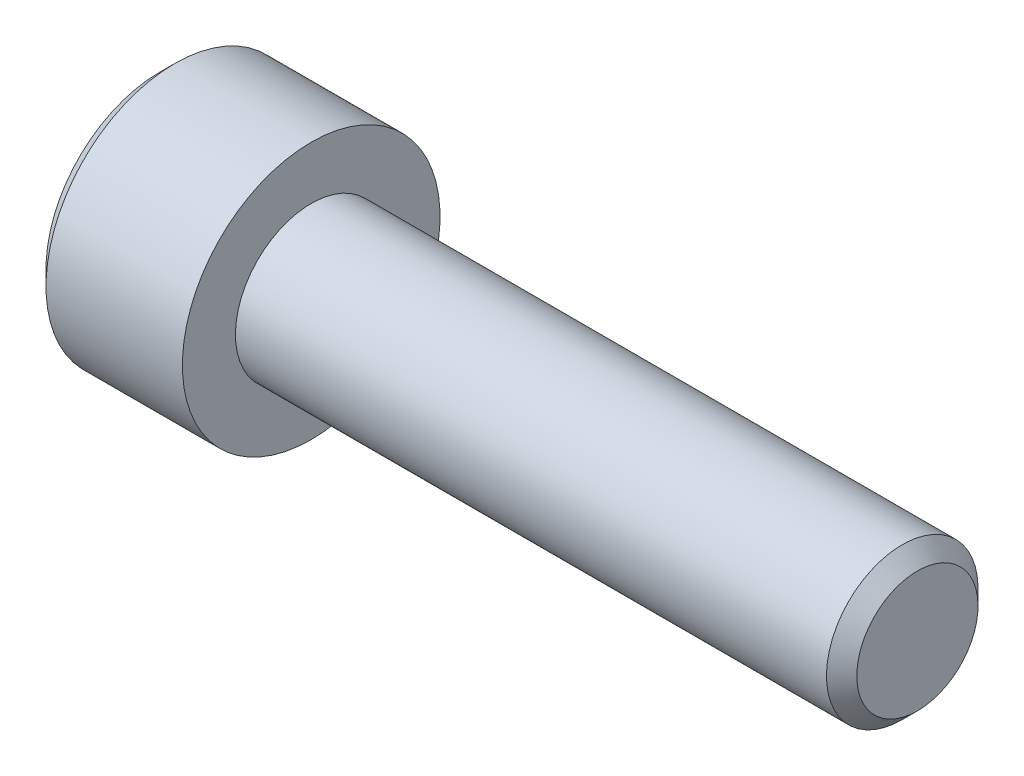
SolidWorks part; units mm, degrees
ref_plane "Front" through (0, 0, 0) normal (0, 0, 1) x (1, 0, 0)
ref_plane "Top" through (0, 0, 0) normal (0, 1, 0) x (1, 0, 0)
ref_plane "Right" through (0, 0, 0) normal (1, 0, 0) x (0, 0, -1)
ref_plane "Plane1" through (0, 0, 0) normal (0, 0, 1) x (1, 0, 0)
sketch "Sketch1" plane through (0, 0, 0) normal (0, 0, 1) x (1, 0, 0)
  line L0 (-5, 0) -> (-5, 3.75)
  line L1 (-5, 3.75) -> (-4.5, 4.25)
  line L2 (-4.5, 4.25) -> (0, 4.25)
  line L3 (0, 4.25) -> (0, 2.5)
  line L4 (0, 2.5) -> (20, 2.5)
  line L6 (20, 2.5) -> (20, 0)
  line L7 (20, 0) -> (-5, 0)
  line L8 (20, 0) -> (-5, 0) construction
  dimension "D1" = 2.5
  dimension "D2" = 20
  dimension "D3" = 5
  dimension "D4" = 4.25
revolve "Revolve1" add sketch "Sketch1" angle 360 about L8
ref_plane "Plane2" through (0, 0, 0) normal (0, 0, 1) x (1, 0, 0)
chamfer "Chamfer1" distance 0.5 angle 45 1 edges at (20, -2.5, 0)
sketch "Sketch2" plane through (0, 0, 0) normal (0, 0, 1) x (1, 0, 0)
  line L0 (-5, 0) -> (-5, 2)
  line L1 (-5, 2) -> (-2.5, 2)
  line L2 (-2.5, 2) -> (-1.9641, 0)
  line L3 (-1.9641, 0) -> (-5, 0)
  line L4 (-1.9641, 0) -> (-5, 0) construction
revolve "Cut-Revolve1" cut sketch "Sketch2" angle 360 about L4
ref_plane "Plane3" through (-5, 0, 0) normal (1, 0, 0) x (0, 0, -1)
sketch "Sketch3" plane through (-5, 0, 0) normal (1, 0, 0) x (0, 0, -1)
  line L0 (-2, 1.1547) -> (-2, -1.1547)
  line L1 (-2, -1.1547) -> (0, -2.3094)
  line L2 (0, -2.3094) -> (2, -1.1547)
  line L3 (2, -1.1547) -> (2, 1.1547)
  line L4 (2, 1.1547) -> (0, 2.3094)
  line L5 (0, 2.3094) -> (-2, 1.1547)
extrude "Cut-Extrude1" cut sketch "Sketch3" along normal blind 2.5
